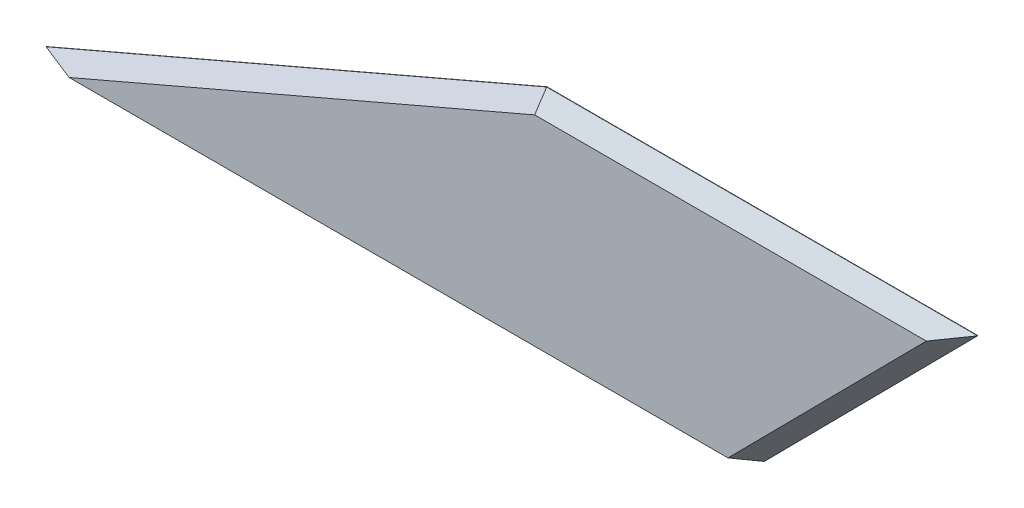
SolidWorks part; units mm, degrees
ref_plane "Alzado" through (0, 0, 0) normal (0, 0, 1) x (1, 0, 0)
ref_plane "Planta" through (0, 0, 0) normal (0, 1, 0) x (1, 0, 0)
ref_plane "Vista lateral" through (0, 0, 0) normal (1, 0, 0) x (0, 0, -1)
sketch "Croquis1" plane through (0, 0, 0) normal (0, 0, 1) x (1, 0, 0)
  line L0 (0, 0) -> (100, 0)
  line L1 (100, 0) -> (129.7, 30)
  line L2 (129.7, 30) -> (69.7, 30)
  line L3 (69.7, 30) -> (0, 0)
  dimension "D1" = 100
  dimension "D2" = 60
  dimension "D3" = 69.7
  dimension "3" = 30
extrude "Saliente-Extruir1" add sketch "Croquis1" along normal mid plane 4.25
sketch "Croquis3" plane through (0, 0, 0) normal (0, -1, 0) x (1, 0, 0)
  line L0 (100, 0) -> (73, 0) construction
  line L1 (100, 2.125) -> (100, -2.125) construction
  circle A0 centre (73, 0) radius 2
  dimension "D1" = 4
  dimension "D2" = 27
extrude "Cortar-Extruir1" cut sketch "Croquis3" against normal blind 10 and the other way through all
chamfer "Chamfer1" distance 2.1 angle 45 6 edges at (114.85, 15, -2.125) (99.7, 30, -2.125) (34.85, 15, -2.125) (114.85, 15, 2.125) (99.7, 30, 2.125) (34.85, 15, 2.125)
